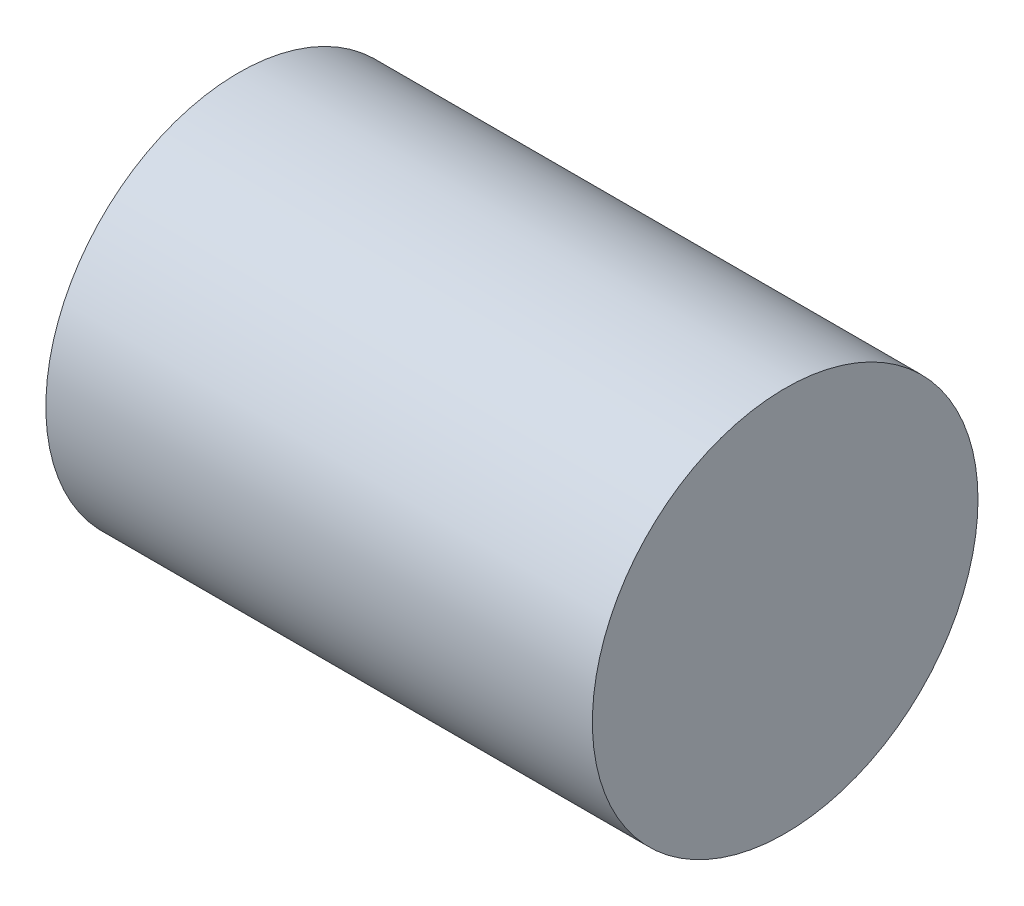
SolidWorks part; units mm, degrees
material "Ceramic Porcelain"
ref_plane "Front Plane" through (0, 0, 0) normal (0, 0, 1) x (1, 0, 0)
ref_plane "Top Plane" through (0, 0, 0) normal (0, 1, 0) x (1, 0, 0)
ref_plane "Right Plane" through (0, 0, 0) normal (1, 0, 0) x (0, 0, -1)
sketch "Sketch2" plane through (0, 0, 0) normal (1, 0, 0) x (0, 0, -1)
  circle A0 centre (0, 0) radius 1.5875
  dimension "D1" = 3.175
extrude "Boss-Extrude1" add sketch "Sketch2" along normal mid plane 4.5
